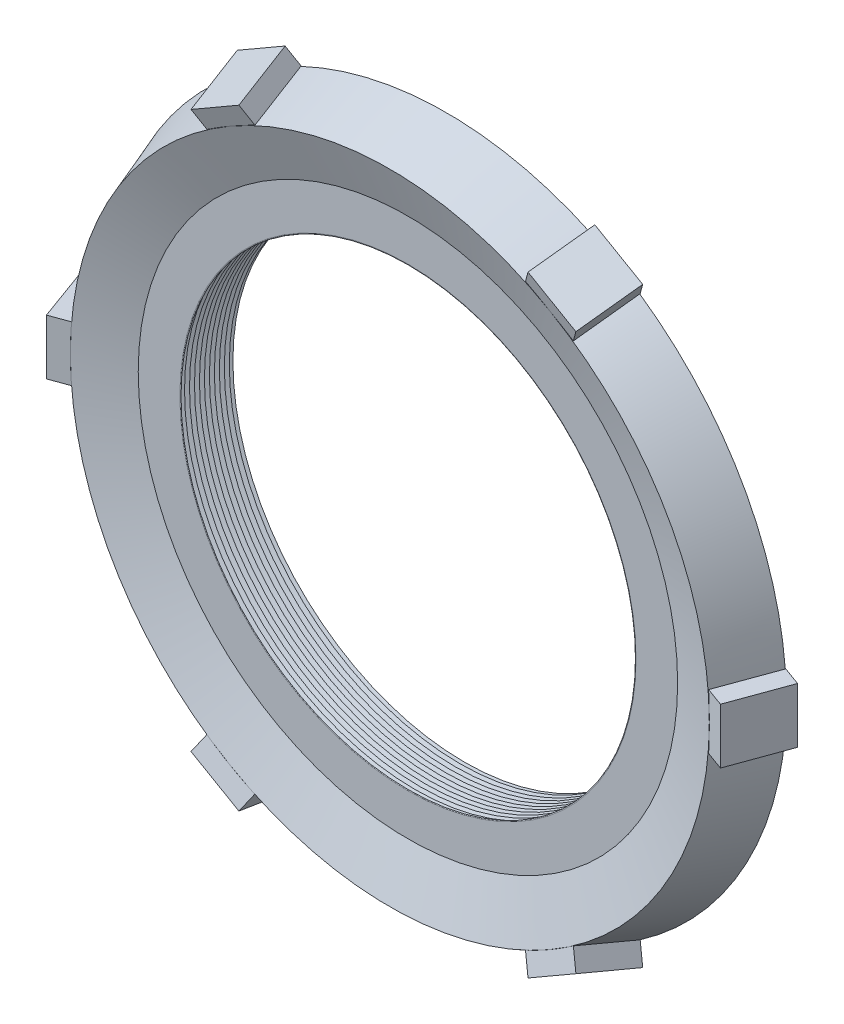
SolidWorks part; units mm, degrees
ref_plane "Front Plane" through (0, 0, 0) normal (0, 0, 1) x (1, 0, 0)
ref_plane "Top Plane" through (0, 0, 0) normal (0, 1, 0) x (1, 0, 0)
ref_plane "Right Plane" through (0, 0, 0) normal (1, 0, 0) x (0, 0, -1)
sketch "Sketch1" plane through (0, 0, 0) normal (0, 1, 0) x (1, 0, 0)
  line L0 (0, 37.8381) -> (0, -37.4672) construction
  line L1 (20.828, 2.54) -> (26.67, 2.54)
  line L2 (26.67, 2.54) -> (31.242, 0.8759)
  line L3 (31.242, 0.8759) -> (29.3516, -4.318)
  line L4 (29.3516, -4.318) -> (24.7796, -2.6539)
  line L5 (24.7796, -2.6539) -> (20.828, -2.6539)
  line L6 (20.828, -2.6539) -> (20.828, 2.54)
  dimension "D1" = 6.858
  dimension "G/2" = 2.54
  dimension "D4" = 20
  dimension "D5" = 4.572
  dimension "D6" = 31.242
  dimension "TS" = 41.656
revolve "Revolve1" add sketch "Sketch1" angle 360 about L0
sketch "Sketch3" plane through (0, 0, 0) normal (0, 1, 0) x (1, 0, 0)
  line L0 (30.226, 1.2457) -> (32.8515, 0.2901)
  line L1 (31.242, 0.8759) -> (26.67, 2.54) construction
  line L2 (32.8515, 0.2901) -> (30.9611, -4.9038)
  line L3 (30.9611, -4.9038) -> (28.3356, -3.9482)
  line L4 (29.3516, -4.318) -> (24.7796, -2.6539) construction
  line L5 (28.3356, -3.9482) -> (30.226, 1.2457)
  dimension "D1" = 30.226
  dimension "D2" = 2.794
extrude "Extrude3" add sketch "Sketch3" along normal blind 2.54 and the other way blind 2.54
pattern_circular "CirPattern1" count 6 over 360 about axis through (0, 0, 0) along (0, 0, 1) of "Extrude3"
fillet "Fillet4" radius 0.127 2 edges at (-20.828, 0, -2.54) (-20.828, 0, 2.6539)
sketch "Sketch4" plane through (0, 0, 0) normal (0, 1, 0) x (1, 0, 0)
  line L0 (-20.828, -2.6539) -> (-20.828, -1.774)
  line L2 (-20.828, -1.774) -> (-21.59, -2.214)
  line L3 (-21.59, -2.214) -> (-20.828, -2.6539)
  line L4 (-24.7796, -2.6539) -> (24.7796, -2.6539) construction
  line L5 (-20.828, 2.413) -> (-20.828, -2.5269) construction
  dimension "D1" = 60
  dimension "D2" = 60
  dimension "D3" = 0.762
revolve "Cut-Revolve1" cut sketch "Sketch4" angle 360 about axis through (0, 0, -37.8381) along (0, 0, 1)
pattern_linear "LPattern1" count 11 spacing 0.4572 along (0, 0, -1) of "Cut-Revolve1"
